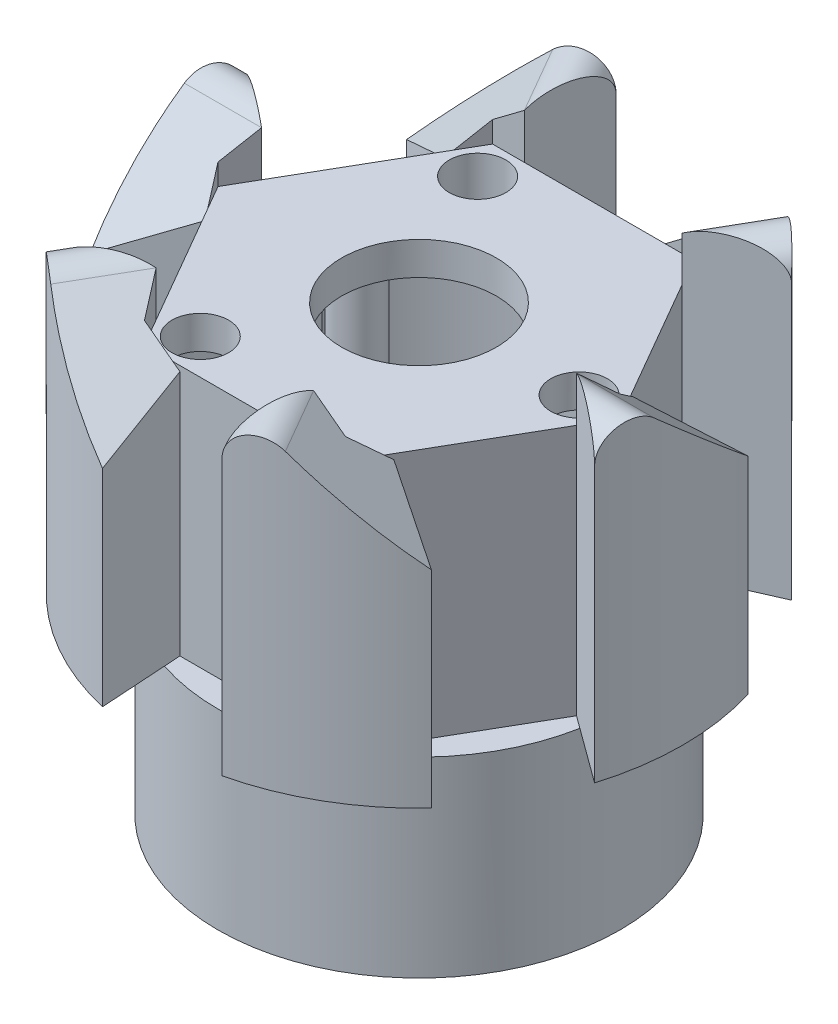
SolidWorks part; units mm, degrees
ref_plane "Front Plane" through (0, 0, 0) normal (0, 0, 1) x (1, 0, 0)
ref_plane "Top Plane" through (0, 0, 0) normal (0, 1, 0) x (1, 0, 0)
ref_plane "Right Plane" through (0, 0, 0) normal (1, 0, 0) x (0, 0, -1)
sketch "Sketch1" plane through (0, 0, 0) normal (0, 1, 0) x (1, 0, 0)
  circle A0 centre (0, 0) radius 6.815
  dimension "D1" = 13.63
extrude "Boss-Extrude1" add sketch "Sketch1" along normal blind 6.49
sketch "Sketch2" plane through (0, 6.49, 0) normal (0, 1, 0) x (1, 0, 0)
  line L0 (-55, 0) -> (55, 0) construction
  line L1 (3.4075, 5.902) -> (-3.4075, 5.902)
  line L2 (-3.4075, 5.902) -> (-6.815, 0)
  line L3 (-6.815, 0) -> (-3.4075, -5.902)
  line L4 (-3.4075, -5.902) -> (3.4075, -5.902)
  line L5 (3.4075, -5.902) -> (6.815, 0)
  line L6 (6.815, 0) -> (3.4075, 5.902)
  circle A0 centre (0, 0) radius 5.902 construction
  circle A1 centre (0, 0) radius 6.815 construction
  point P11 (0, 0)
extrude "Boss-Extrude2" add sketch "Sketch2" along normal blind 8.53
sketch "Sketch3" plane through (0, 0, 0) normal (1, 0, 0) x (0, 0, -1)
  line L0 (-2.6, 6.49) -> (2.6, 6.49)
  line L1 (0, 6.49) -> (-5.902, 6.49) construction
  line L2 (5.902, 6.49) -> (0, 6.49) construction
  line L3 (2.6, 6.49) -> (2.6, 13.49)
  line L4 (-2.6, 6.49) -> (-2.6, 13.49)
  line L5 (0, 7.4965) -> (0, -7.4965) construction
  line L8 (2.6, 13.49) -> (-0.9347, 16.55)
  line L9 (-2.6, 13.49) -> (-2.6, 15.789)
  line L10 (0, 15.7409) -> (4.5486, 15.7409) construction
  arc A1 (-2.6, 15.789) -> (-0.9347, 16.55) centre (-1.5935, 15.789) cw
  dimension "D1" = 2.6
  dimension "D2" = 2.6
  dimension "D3" = 7
  dimension "D4" = 7
  dimension "D5" = 3.06
extrude "Boss-Extrude3" add sketch "Sketch3" along normal blind 10
pattern_circular "CirPattern1" count 6 over 360 about axis through (0, 0, 0) along (0, 1, 0) of "Boss-Extrude3"
sketch "Sketch4" plane through (0, 0, 0) normal (0, 1, 0) x (1, 0, 0)
  circle A0 centre (0, 0) radius 8.94
  circle A1 centre (0, 0) radius 10.9144
  dimension "D1" = 17.88
extrude "Cut-Extrude1" cut sketch "Sketch4" along normal blind 18
sketch "Sketch5" plane through (0, 15.02, 0) normal (0, 1, 0) x (1, 0, 0)
  line L0 (2.446, 5.902) -> (-0.4053, 5.902) construction
  line L1 (-3.4075, 5.902) -> (-6.815, 0)
  line L2 (-6.815, 0) -> (-3.4075, -5.902)
  line L3 (-3.4075, -5.902) -> (3.4075, -5.902)
  line L4 (3.4075, -5.902) -> (6.815, 0)
  line L5 (6.815, 0) -> (3.4075, 5.902)
  line L6 (3.4075, 5.902) -> (-3.4075, 5.902)
  circle A0 centre (0, 0) radius 5.902 construction
extrude "Cut-Extrude2" cut sketch "Sketch5" along normal blind 18
sketch "Sketch6" plane through (0, 0, 0) normal (0, 1, 0) x (1, 0, 0)
  line L0 (-8.5536, -2.6) -> (-6.687, -1.3144)
  line L1 (-7.4965, 0) -> (7.4965, 0) construction
  line L2 (-8.5536, 2.6) -> (-6.687, 1.3144)
  line L3 (-8.5536, -2.6) -> (-6.2995, -2.6)
  line L4 (-8.5536, 2.6) -> (-6.2995, 2.6)
  arc A1 (-6.2995, 2.6) -> (-6.2995, -2.6) centre (0, 0) ccw construction
  arc A2 (-6.2995, 2.6) -> (-6.687, 1.3144) centre (0, 0) ccw
  arc A3 (-6.2995, -2.6) -> (-6.687, -1.3144) centre (0, 0) cw
sketch "Sketch7" plane through (0, 6.49, 0) normal (0, 1, 0) x (1, 0, 0)
  line L0 (-6.2138, -1.0412) -> (-8.5536, -2.6)
  line L1 (-8.5536, -2.6) -> (-5.3139, -2.6)
  line L2 (-8.5536, 2.6) -> (-6.2754, 0.9347)
  line L3 (-8.5536, 2.6) -> (-5.3139, 2.6)
  line L4 (-6.2754, 0.9347) -> (-5.3139, 2.6)
  line L5 (-5.3139, -2.6) -> (-6.3343, -0.8327) construction
  line L6 (-6.2138, -1.0412) -> (-5.3139, -2.6)
extrude "Cut-Extrude4" cut sketch "Sketch7" along normal through all
pattern_circular "CirPattern2" count 6 over 360 about axis through (0, 0, 0) along (0, 1, 0) of "Cut-Extrude4"
sketch "Sketch8" plane through (0, 15.02, 0) normal (0, 1, 0) x (1, 0, 0)
  circle A0 centre (0, 0) radius 2.625
  dimension "D1" = 5.25
extrude "Cut-Extrude5" cut sketch "Sketch8" against normal through all and the other way through all
sketch "Sketch9" plane through (0, 0, 0) normal (0, -1, 0) x (-1, 0, 0)
  circle A0 centre (0, 0) radius 5.84
  dimension "D1" = 11.68
extrude "Cut-Extrude6" cut sketch "Sketch9" against normal blind 13.9
sketch "Sketch10" plane through (0, 0, 0) normal (0, 1, 0) x (1, 0, 0)
  line L1 (0, -7.4965) -> (0, 7.4965) construction
  line L2 (-0.7909, -5.84) -> (0.7909, -5.84)
  arc A0 (-0.7909, -5.84) -> (0.7909, -5.84) centre (0, -5.84) cw
  circle A2 centre (0, 0) radius 5.84 construction
extrude "Boss-Extrude4" add sketch "Sketch10" along normal up to surface (13.9 mm away) up to face at (0, 13.9, -5.84)
pattern_circular "CirPattern3" count 3 over 360 about axis through (0, 0, 0) along (0, 1, 0) of "Boss-Extrude4"
sketch "Sketch11" plane through (0, 13.9, 0) normal (0, -1, 0) x (1, 0, 0)
  line L4 (1.1049, 5.7535) -> (0.983, 5.3355)
  line L5 (0.983, 5.3355) -> (1.6867, 5.1302)
  line L6 (1.6867, 5.1302) -> (1.8116, 5.5583)
  line L9 (1.1049, 5.7535) -> (1.8116, 5.5583)
  arc A2 (5.4057, -2.2099) -> (0.7891, 5.7864) centre (0, 0) ccw construction
  point P2 (1.073, 5.3678)
extrude "Boss-Extrude5" add sketch "Sketch11" along normal offset from surface (13.4 mm away) 0.5 up to face at (0, 0, 0)
pattern_circular "CirPattern4" count 3 over 360 about axis through (0, 0, 0) along (0, 1, 0) of "Boss-Extrude5"
sketch "Sketch12" plane through (0, 15.02, 0) normal (0, 1, 0) x (1, 0, 0)
  line L0 (-3.4075, -5.902) -> (-2.446, -5.902) construction
  line L1 (-6.2138, -1.0412) -> (-3.9471, -4.9673) construction
  line L2 (-4.0087, 4.8607) -> (-6.2754, 0.9347) construction
  line L3 (2.2052, 5.902) -> (-2.3282, 5.902) construction
  line L4 (6.2138, 1.0412) -> (3.9471, 4.9673) construction
  line L5 (3.8882, -5.0693) -> (6.2754, -0.9347) construction
  circle A0 centre (-2.7143, -4.7027) radius 0.96
  circle A1 centre (-2.7147, 4.702) radius 0.96
  circle A2 centre (5.4294, 0) radius 0.96
  point P18 (0, 0)
  dimension "D1" = 1.92
  dimension "D4" = 1.92
  dimension "D7" = 1.92
  dimension "D8" = 1.2
  dimension "D2" = 1.1993
  dimension "D3" = 1.2
  dimension "D5" = 1.2
  dimension "D6" = 1.2
  dimension "D9" = 1.2
extrude "Cut-Extrude7" cut sketch "Sketch12" against normal blind 3.25
